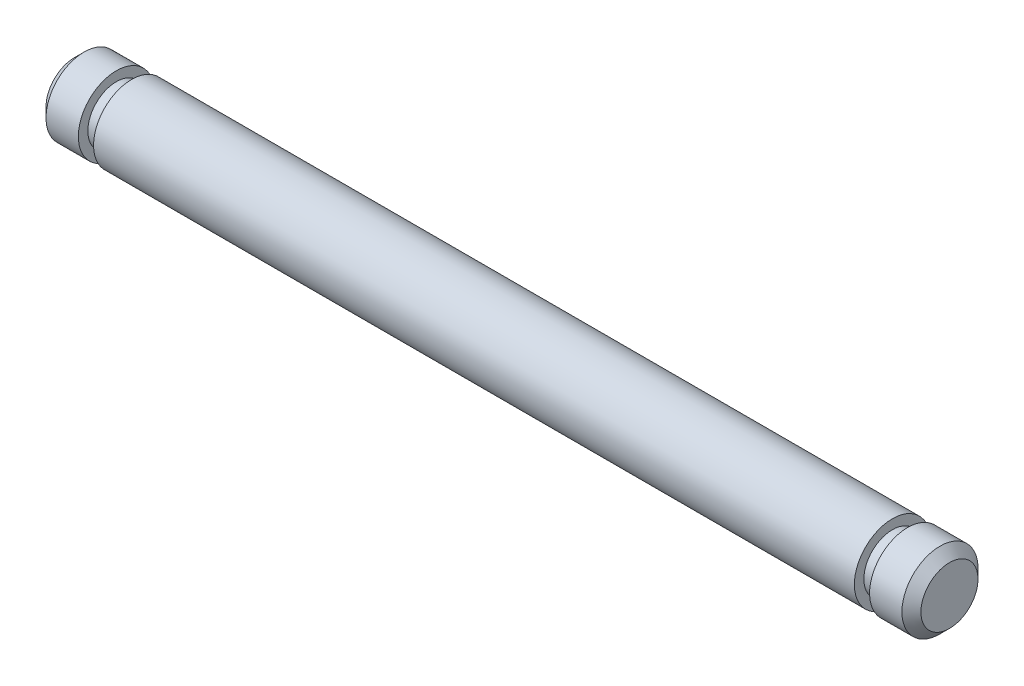
SolidWorks part; units mm, degrees
material "Ductile Iron (SN)"
ref_plane "Front Plane" through (0, 0, 0) normal (0, 0, 1) x (1, 0, 0)
ref_plane "Top Plane" through (0, 0, 0) normal (0, 1, 0) x (1, 0, 0)
ref_plane "Right Plane" through (0, 0, 0) normal (1, 0, 0) x (0, 0, -1)
sketch "Sketch1" plane through (0, 0, 0) normal (0, 0, 1) x (1, 0, 0)
  line L0 (0, 0) -> (46, 0)
  line L1 (46, 0) -> (46, 2)
  line L2 (46, 2) -> (0, 2)
  line L3 (0, 2) -> (0, 0)
  dimension "D1" = 46
  dimension "D2" = 2
revolve "Revolve2" add sketch "Sketch1" angle 360 about L2
sketch "Sketch2" plane through (46, 0, 0) normal (1, 0, 0) x (0, 0, -1)
  circle A0 centre (0, 2) radius 1.5
  circle A1 centre (0, 2) radius 2
  circle A2 centre (0, 2) radius 2
  dimension "D2" = 3
  dimension "D1" = 0
extrude "Cut-Extrude1" cut sketch "Sketch2" along normal blind 0.8 from offset 3 offset against normal yes
sketch "Sketch3" plane through (0, 0, 0) normal (-1, 0, 0) x (0, 0, 1)
  circle A0 centre (0, 2) radius 2 construction
  circle A1 centre (0, 2) radius 2
  circle A2 centre (0, 2) radius 1.5
  dimension "D1" = 3
extrude "Cut-Extrude3" cut sketch "Sketch3" along normal blind 0.8 from offset 3 offset against normal yes
chamfer "Chamfer1" distance 0.5 angle 45 2 edges at (0, 4, 0) (46, 4, 0)
